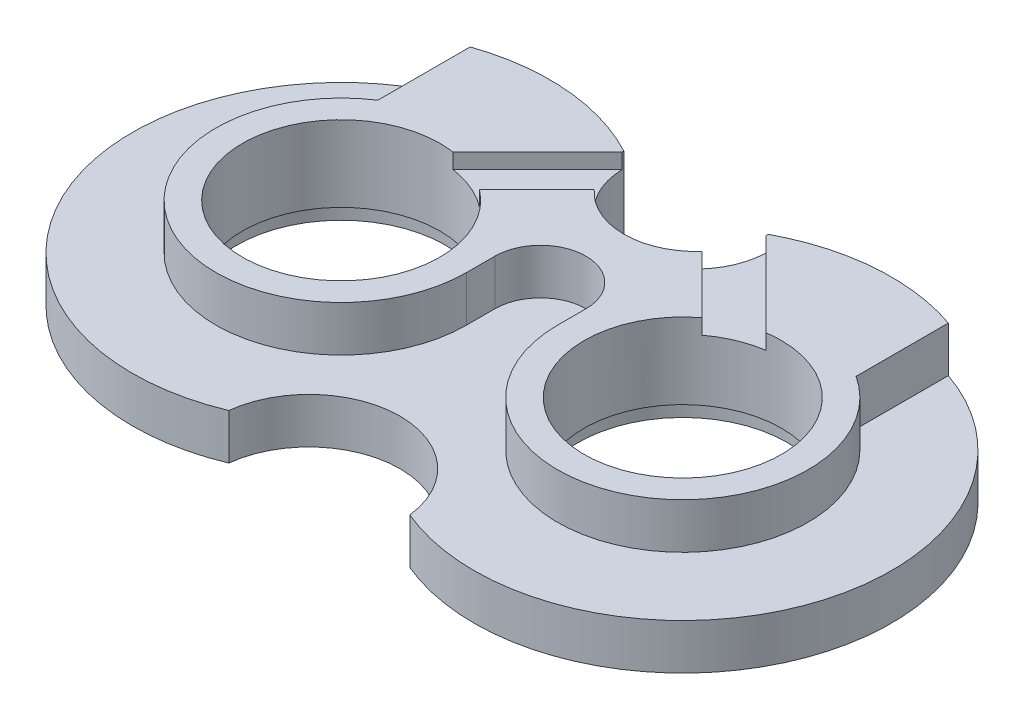
SolidWorks part; units mm, degrees
material "АЛ8Т4 ГОСТ 1583-93"
ref_plane "Спереди" through (0, 0, 0) normal (0, 0, 1) x (1, 0, 0)
ref_plane "Сверху" through (0, 0, 0) normal (0, 1, 0) x (1, 0, 0)
ref_plane "Справа" through (0, 0, 0) normal (1, 0, 0) x (0, 0, -1)
sketch "Эскиз1" plane through (0, 0, 0) normal (0, 1, 0) x (1, 0, 0)
  line L0 (0, 0) -> (0, 15.8114) construction
  arc A0 (0, -15.8114) -> (0, 15.8114) centre (22.5, 0) ccw
  arc A1 (0, 15.8114) -> (0, -15.8114) centre (-22.5, 0) ccw
  point P4 (-50, 0)
  point P5 (50, 0)
  dimension "D2" = 55
  dimension "D3" = 100
extrude "Бобышка-Вытянуть1" add sketch "Эскиз1" along normal blind 12
sketch "Эскиз2" plane through (0, 0, 0) normal (0, 1, 0) x (1, 0, 0)
  circle A0 centre (0, 24.25) radius 9.5
  circle A1 centre (0, -26.75) radius 12
  point P4 (0, 14.75)
  point P5 (0, -14.75)
  dimension "D1" = 19
  dimension "D2" = 24
  dimension "D3" = 29.5
  dimension "D4" = 14.75
extrude "Вырез-Вытянуть1" cut sketch "Эскиз2" along normal through all
sketch "Эскиз3" plane through (0, 12, 0) normal (0, 1, 0) x (1, 0, 0)
  line L0 (-6, 0) -> (-6, 3.75)
  line L1 (31.5, 40) -> (31.5, 13.8293)
  line L2 (6, 0) -> (6, 3.75)
  line L3 (-31.5, 40) -> (-31.5, 13.8293)
  line L4 (-31.5, 40) -> (-71.5, 40)
  line L5 (-71.5, 40) -> (-71.5, -30)
  line L6 (-71.5, -30) -> (71.5, -30)
  line L7 (71.5, -30) -> (71.5, 40)
  line L8 (71.5, 40) -> (31.5, 40)
  arc A0 (-31.5, 13.8293) -> (-6, 0) centre (-22.5, 0) ccw
  arc A1 (6, 0) -> (31.5, 13.8293) centre (22.5, 0) ccw
  arc A2 (-6, 3.75) -> (6, 3.75) centre (0, 3.75) cw
  arc A3 (-9.5, 24.2332) -> (9.5, 24.2332) centre (0, 24.25) ccw construction
  point P11 (0, 9.75)
  point P12 (0, 14.75)
  dimension "D1" = 33
  dimension "D2" = 33
  dimension "D3" = 5
  dimension "D4" = 31.5
  dimension "D5" = 31.5
  dimension "D6" = 70
  dimension "D7" = 40
  dimension "D8" = 40
  dimension "D9" = 30
extrude "Вырез-Вытянуть2" cut sketch "Эскиз3" against normal blind 6
sketch "Эскиз4" plane through (0, 0, 0) normal (0, 1, 0) x (1, 0, 0)
  circle A0 centre (-22.5, 0) radius 13
  circle A1 centre (22.5, 0) radius 13
  dimension "D1" = 26
  dimension "D2" = 26
extrude "Вырез-Вытянуть3" cut sketch "Эскиз4" along normal through all
sketch "Эскиз7" plane through (0, 0, 0) normal (0, -1, 0) x (1, 0, 0)
  circle A0 centre (-22.5, 0) radius 13.75
  circle A1 centre (22.5, 0) radius 13.75
  dimension "D1" = 27.5
  dimension "D2" = 27.5
extrude "Вырез-Вытянуть5" cut sketch "Эскиз7" against normal blind 2
sketch "Эскиз8" plane through (0, 12, 0) normal (0, 1, 0) x (1, 0, 0)
  line L0 (-9.2426, 24.2426) -> (-26.9203, 6.565)
  line L1 (-26.9203, 6.565) -> (-22.6777, 2.3223)
  line L2 (-22.6777, 2.3223) -> (-5, 20)
  line L3 (-5, 20) -> (-9.2426, 24.2426)
  line L4 (9.2426, 24.2426) -> (26.9203, 6.565)
  line L5 (26.9203, 6.565) -> (22.6777, 2.3223)
  line L6 (22.6777, 2.3223) -> (5, 20)
  line L7 (5, 20) -> (9.2426, 24.2426)
  line L8 (0, 0) -> (0, 30) construction
  line L9 (0, 30) -> (-105.2483, 30) construction
  dimension "D1" = 6
  dimension "D2" = 6
  dimension "D3" = 45
  dimension "D4" = 45
  dimension "D5" = 25
  dimension "D6" = 25
  dimension "D7" = 5
  dimension "D8" = 10
  dimension "D9" = 30
extrude "Вырез-Вытянуть6" cut sketch "Эскиз8" against normal blind 2
